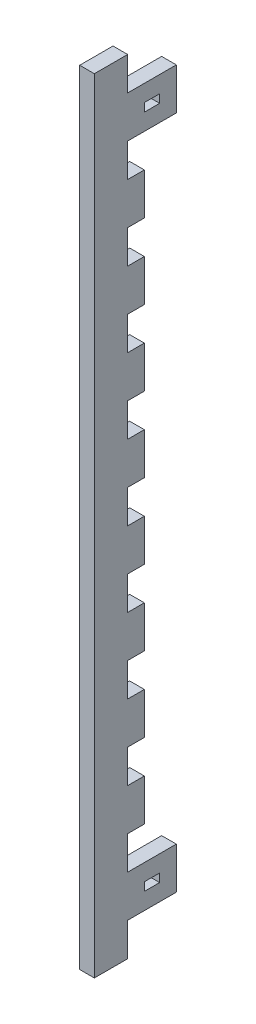
SolidWorks part; units mm, degrees
material "Acrylic (Medium-high impact)"
ref_plane "Front" through (0, 0, 0) normal (0, 0, 1) x (1, 0, 0)
ref_plane "Top" through (0, 0, 0) normal (0, 1, 0) x (1, 0, 0)
ref_plane "Right" through (0, 0, 0) normal (1, 0, 0) x (0, 0, -1)
sketch "Sketch1" plane through (0, 0, 0) normal (1, 0, 0) x (0, 0, -1)
  line L0 (9.525, 120.65) -> (9.525, 107.95)
  line L1 (-9.525, 149.225) -> (9.525, 149.225)
  line L2 (-9.525, 149.225) -> (-9.525, -149.225)
  line L3 (-9.525, -149.225) -> (9.525, -149.225)
  line L4 (9.525, 149.225) -> (9.525, -149.225)
  line L17 (9.525, 149.225) -> (3.175, 149.225)
  line L22 (9.525, 149.225) -> (9.525, 136.525)
  line L27 (9.525, 136.525) -> (3.175, 136.525)
  line L32 (3.175, 149.225) -> (3.175, 136.525)
  line L37 (9.525, 120.65) -> (3.175, 120.65)
  line L42 (3.175, 120.65) -> (3.175, 107.95)
  line L47 (9.525, 107.95) -> (3.175, 107.95)
  line L52 (9.525, 92.075) -> (9.525, 79.375)
  line L57 (9.525, 92.075) -> (3.175, 92.075)
  line L62 (3.175, 92.075) -> (3.175, 79.375)
  line L67 (9.525, 79.375) -> (3.175, 79.375)
  line L68 (9.525, 63.5) -> (9.525, 50.8)
  line L72 (9.525, 63.5) -> (3.175, 63.5)
  line L73 (3.175, 63.5) -> (3.175, 50.8)
  line L78 (9.525, 50.8) -> (3.175, 50.8)
  line L79 (9.525, 34.925) -> (9.525, 22.225)
  line L80 (9.525, 34.925) -> (3.175, 34.925)
  line L81 (3.175, 34.925) -> (3.175, 22.225)
  line L82 (9.525, 22.225) -> (3.175, 22.225)
  line L83 (9.525, 6.35) -> (9.525, -6.35)
  line L84 (9.525, 6.35) -> (3.175, 6.35)
  line L85 (3.175, 6.35) -> (3.175, -6.35)
  line L86 (9.525, -6.35) -> (3.175, -6.35)
  line L87 (9.525, -22.225) -> (9.525, -34.925)
  line L88 (9.525, -22.225) -> (3.175, -22.225)
  line L89 (3.175, -22.225) -> (3.175, -34.925)
  line L90 (9.525, -34.925) -> (3.175, -34.925)
  line L91 (9.525, -50.8) -> (9.525, -63.5)
  line L92 (9.525, -50.8) -> (3.175, -50.8)
  line L93 (3.175, -50.8) -> (3.175, -63.5)
  line L94 (9.525, -63.5) -> (3.175, -63.5)
  line L95 (9.525, -79.375) -> (9.525, -92.075)
  line L96 (9.525, -79.375) -> (3.175, -79.375)
  line L97 (3.175, -79.375) -> (3.175, -92.075)
  line L98 (9.525, -92.075) -> (3.175, -92.075)
  line L99 (9.525, -107.95) -> (9.525, -120.65)
  line L100 (9.525, -107.95) -> (3.175, -107.95)
  line L101 (3.175, -107.95) -> (3.175, -120.65)
  line L102 (9.525, -120.65) -> (3.175, -120.65)
  line L103 (9.525, -136.525) -> (9.525, -149.225)
  line L104 (9.525, -136.525) -> (3.175, -136.525)
  line L105 (3.175, -136.525) -> (3.175, -149.225)
  line L106 (9.525, -149.225) -> (3.175, -149.225)
  point P4 (0, -149.225)
  point P6 (-9.525, 0)
  dimension "D1" = 19.05
  dimension "D2" = 298.45
  dimension "D3" = 12.7
  dimension "D4" = 6.35
  dimension "D5" = 11
extrude "Boss-Extrude1" add sketch "Sketch1" along normal blind 5.588
sketch "Sketch2" plane through (5.588, 0, 0) normal (1, 0, 0) x (0, 0, -1)
  line L0 (9.525, 120.65) -> (3.175, 120.65) construction
  line L1 (9.525, 136.525) -> (21.717, 136.525)
  line L2 (9.525, 136.525) -> (9.525, 120.65)
  line L3 (9.525, 120.65) -> (21.717, 120.65)
  line L4 (21.717, 136.525) -> (21.717, 120.65)
  line L5 (9.525, -136.525) -> (3.175, -136.525) construction
  line L6 (9.525, -120.65) -> (21.717, -120.65)
  line L7 (9.525, -120.65) -> (9.525, -136.525)
  line L8 (9.525, -136.525) -> (21.717, -136.525)
  line L9 (21.717, -120.65) -> (21.717, -136.525)
  line L11 (9.525, -127) -> (15.367, -127)
  line L12 (9.525, -127) -> (9.525, -130.175)
  line L13 (9.525, -130.175) -> (15.367, -130.175)
  line L14 (15.367, -127) -> (15.367, -130.175)
  line L15 (9.525, 130.175) -> (15.367, 130.175)
  line L16 (9.525, 130.175) -> (9.525, 127)
  line L17 (9.525, 127) -> (15.367, 127)
  line L18 (15.367, 130.175) -> (15.367, 127)
  point P22 (15.367, -128.5875)
  point P23 (21.717, 128.5875)
  point P26 (15.367, 128.5875)
  point P27 (21.717, -128.5875)
  line M21 (9.525, -136.525) -> (9.525, -120.65)
  line M57 (9.525, 120.65) -> (9.525, 136.525)
  dimension "D1" = 6.35
  dimension "D3" = 3.175
  dimension "D4" = 5.842
extrude "Boss-Extrude2" add sketch "Sketch2" against normal up to surface (5.588 mm away) contours L11 L14 L13 L8 L9 L6 L7 M21 | L15 L18 L17 L3 L4 L1 L2 M57 up to face at (0, 0, -5.4841)
